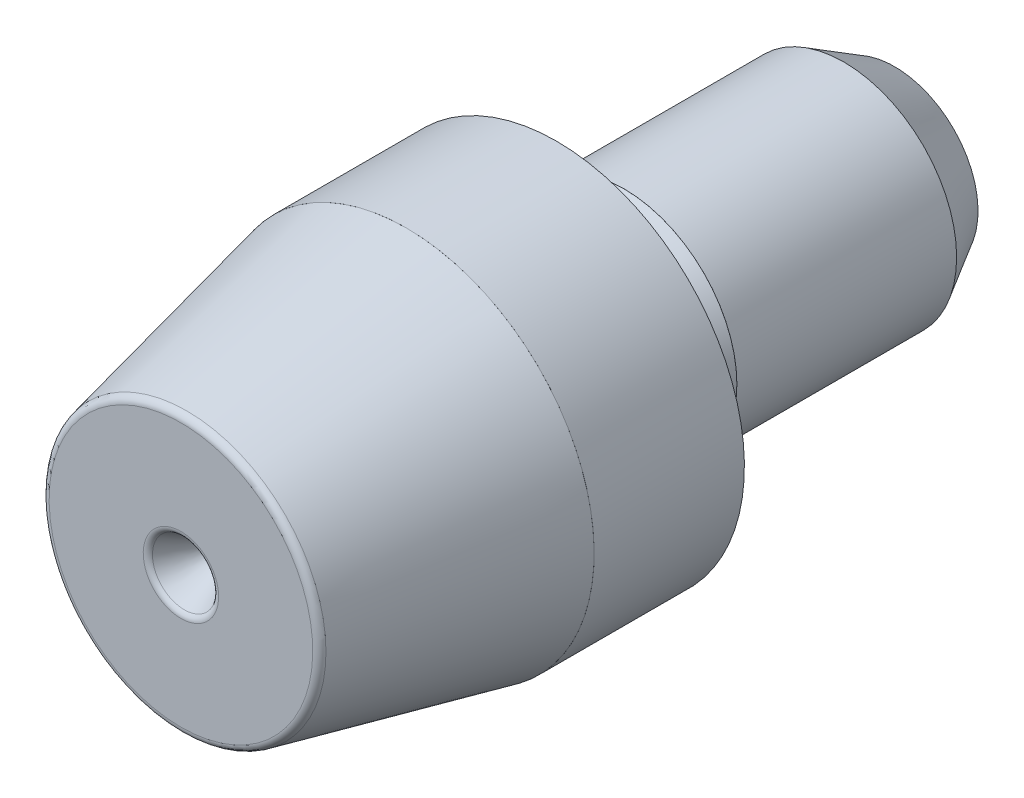
SolidWorks part; units mm, degrees
ref_plane "Front" through (0, 0, 0) normal (0, 0, 1) x (1, 0, 0)
ref_plane "Top" through (0, 0, 0) normal (0, 1, 0) x (1, 0, 0)
ref_plane "Right" through (0, 0, 0) normal (1, 0, 0) x (0, 0, -1)
sketch "Sketch1" plane through (0, 0, 0) normal (1, 0, 0) x (0, 0, -1)
  line L0 (-9.5, 0) -> (9.5, 0) construction
  line L1 (-9.5, -5) -> (-9.5, 5) construction
  line L2 (9.5, -3) -> (9.5, 3) construction
  line L3 (-9.5, 0) -> (0.5, 0) construction
  line L4 (-9.5, 0) -> (-3.5, 0) construction
  line L5 (9.5, 3) -> (0.5, 3) construction
  line L6 (-3.5, 5) -> (-9.5, 3.6698) construction
  line L7 (-3.5, 5) -> (0.5, 5) construction
  line L8 (0.5, 5) -> (0.5, 3) construction
  point P3 (0.5, -3)
  point P4 (0, 0)
  point P7 (-9.5, 0)
  point P11 (9.5, 0)
  point P14 (-3.5, 5)
  point P18 (-9.5, 3.6698)
  point P19 (0.5, 5)
  point P20 (0.5, 3)
  point P21 (0.5, -5)
  point P22 (-3.5, -5)
  point P23 (-9.5, -3.6698)
  dimension "Overall Height" = 19
  dimension "Head Diameter" = 10
  dimension "Shank Diameter" = 6
  dimension "Head Height" = 10
  dimension "Head End Height" = 6
  dimension "D1" = 12.5
  dimension "D2" = 9
sketch "Sketch2" plane through (0, 0, 0) normal (0, 0, 1) x (1, 0, 0)
  line L0 (-4.3819, 0) -> (-1.6586, 4.7169) construction
  line L1 (-4.3819, 0) -> (-1.6586, -4.7169) construction
  line L2 (1.6586, 4.7169) -> (4.3819, 0) construction
  line L3 (4.3819, 0) -> (1.6586, -4.7169) construction
  line L4 (-4.3819, 0) -> (4.3819, 0) construction
  line L5 (3.2864, 1.8974) -> (3.1782, 1.8349) construction
  line L6 (1.4802, 4.7759) -> (4.2376, 0) construction
  circle A0 centre (0, 0) radius 5 construction
  circle A1 centre (0, 0) radius 0.9 construction
  circle A2 centre (0, 0) radius 4.3819 construction
  circle A3 centre (0, 0) radius 3.6698 construction
  point P13 (0, 0)
  dimension "D2" = 1.8
  dimension "D1" = 60
  dimension "D3" = 0.125
sketch "Sketch3" plane through (0, 0, 0) normal (1, 0, 0) x (0, 0, -1)
  line L0 (-9.5, 0) -> (-9.5, 3.6698)
  line L1 (-9.5, 3.6698) -> (-3.5, 5)
  line L2 (-3.5, 5) -> (0.5, 5)
  line L3 (0.5, 5) -> (0.5, 3)
  line L4 (0.5, 3) -> (9.5, 3)
  line L5 (9.5, 3) -> (9.5, 0)
  line L6 (9.5, 0) -> (-9.5, 0)
  line L7 (9.5, 3) -> (0.5, 3) construction
revolve "Revolve2" add sketch "Sketch3" angle 360 about L6
sketch "Sketch14" plane through (0, 0, -0.5) normal (0, 0, -1) x (-1, 0, 0)
  line L0 (-4.3819, 0) -> (-1.6586, -4.7169) construction
  line L1 (-1.6586, 4.7169) -> (-4.3819, 0) construction
  line L2 (-4.3819, 0) -> (-1.6586, -4.7169)
  line L3 (-1.6586, 4.7169) -> (-4.3819, 0)
  line L5 (-7.3819, 9.4338) -> (-7.3819, -9.4338)
  line L7 (-1.6586, 4.7169) -> (1.0647, 9.4338)
  line L8 (1.0647, 9.4338) -> (-7.3819, 9.4338)
  line L9 (4.3819, 0) -> (-4.3819, 0) construction
  line L10 (-4.3819, 0) -> (-7.3819, 0) construction
  line L11 (-7.3819, -9.4338) -> (1.0647, -9.4338)
  line L12 (1.0647, -9.4338) -> (-1.6586, -4.7169)
  arc A1 (-1.6586, -4.7169) -> (-1.6586, 4.7169) centre (0, 0) ccw construction
  circle A2 centre (0, 0) radius 5 construction
  dimension "D1" = 3
sketch "Sketch16" plane through (0, 0, 0) normal (1, 0, 0) x (0, 0, -1)
  line L0 (0.5, 3) -> (0.3917, 2.8125)
  line L1 (0.5, 5) -> (0.5, 3) construction
  line L2 (0.5, 2.625) -> (1.1375, 2.625)
  line L3 (1.394, 2.6702) -> (2.3, 3)
  line L4 (9.5, 3) -> (0.5, 3) construction
  line L5 (2.3, 3) -> (0.5, 3)
  line L7 (0.5, -3) -> (0.5, 3) construction
  line L8 (9.5, -3) -> (9.5, 3) construction
  line L9 (8.15, 3) -> (9.5, 2.2206)
  line L10 (9.5, 2.2206) -> (9.5, 3)
  line L11 (9.5, 3) -> (8.15, 3)
  line L13 (0.5, -5) -> (0.5, 5) construction
  arc A0 (0.3917, 2.8125) -> (0.5, 2.625) centre (0.5, 2.75) ccw
  arc A1 (1.1375, 2.625) -> (1.394, 2.6702) centre (1.1375, 3.375) ccw
  dimension "D4" = 0.75
  dimension "D1" = 1.8
  dimension "D2" = 1.35
  dimension "D6" = 20
  dimension "D5" = 0.375
  dimension "D8" = 30
  dimension "D3" = 30
revolve "Cut-Revolve1" cut sketch "Sketch16" angle 360 about L0
sketch "Sketch10" plane through (0, 0, 9.5) normal (0, 0, 1) x (1, 0, 0)
  circle A0 centre (0, 0) radius 0.9 construction
  circle A1 centre (0, 0) radius 0.9
extrude "Cut-Extrude2" cut sketch "Sketch10" against normal blind 1.5 draft 30
sketch "Sketch15" plane through (0, 0, -9.5) normal (0, 0, -1) x (-1, 0, 0)
  circle A0 centre (0, 0) radius 0.9 construction
  circle A1 centre (0, 0) radius 0.9
extrude "Cut-Extrude5" cut sketch "Sketch15" against normal blind 1.5 draft 30
fillet "Fillet1" radius 0.2 1 edges at (0, 3.6698, 9.5)
fillet "Fillet3" radius 0.18 2 edges at (0, 0.9, -9.5) (0.9, 0, 9.5)
sketch "Sketch17" plane through (0, 0, -0.5) normal (0, 0, -1) x (-1, 0, 0)
  circle A0 centre (0, 0) radius 5 construction
  circle A1 centre (0, 0) radius 5
  circle A2 centre (0, 0) radius 5.001
  dimension "D1" = 0.001
extrude "Boss-Extrude1" add sketch "Sketch17" against normal up to vertex (4 mm away) separate body up to point (0, 5, 3.5)
ref_plane "Plane1" through (0, 0, -8.15) normal (0, 0, -1) x (-1, 0, 0)
sketch "Sketch19" plane through (0, 0, -8.15) normal (0, 0, -1) x (-1, 0, 0)
  circle A0 centre (0, 0) radius 3 construction
  circle A1 centre (0, 0) radius 3
  circle A2 centre (0, 0) radius 3.001
  dimension "D1" = 0.001
extrude "Boss-Extrude2" add sketch "Sketch19" against normal up to vertex (5.85 mm away) separate body up to point (0, 3, -2.3)
equation "\"D2@Sketch2\"=\"Shank Diameter@Sketch1\"*.3"
equation "\"D1@Fillet1\"=\"Head Diameter@Sketch1\"*.02"
equation "\"D1@Cut-Extrude2\"=\"Head Diameter@Sketch1\"*.15"
equation "\"D1@Cut-Extrude5\"=\"Head Diameter@Sketch1\"*.15"
equation "\"D1@Sketch16\"=\"D2@Sketch1\"*.2"
equation "\"D2@Sketch16\"=\"D2@Sketch1\"*.15"
equation "\"D5@Sketch16\"=\"Shank Diameter@Sketch1\"*.0625"
equation "\"D4@Sketch16\"=\"D5@Sketch16\"*2"
equation "\"D1@Fillet3\"=\"D2@Sketch2\"*.1"
equation "\"D3@Sketch2\"=\"Head Diameter@Sketch1\"*.0125"
